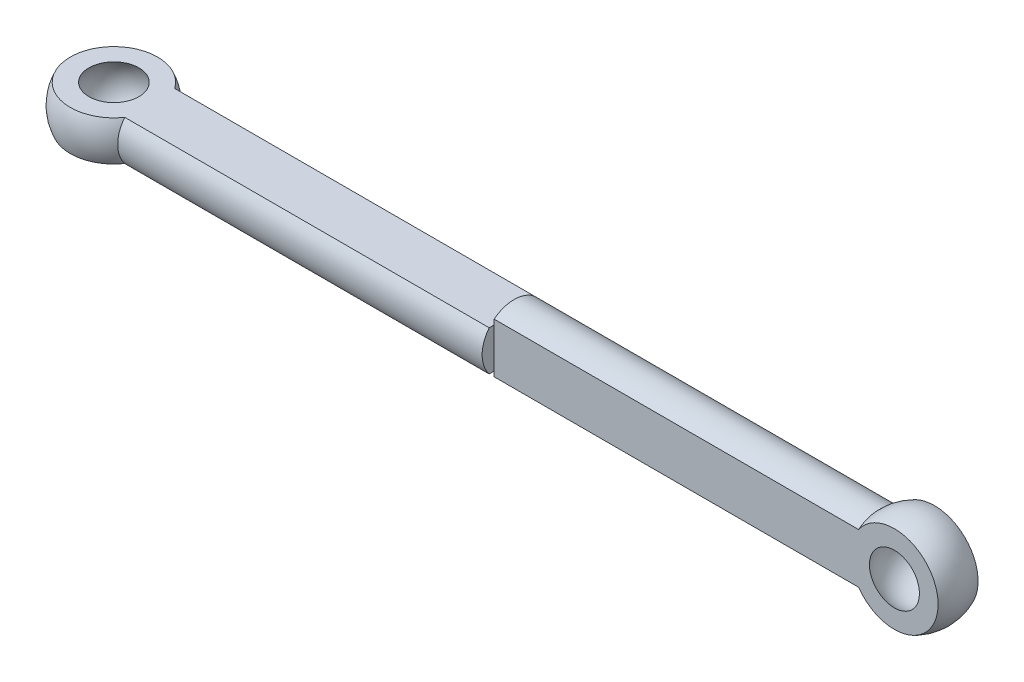
SolidWorks part; units mm, degrees
ref_plane "Front Plane" through (0, 0, 0) normal (0, 0, 1) x (1, 0, 0)
ref_plane "Top Plane" through (0, 0, 0) normal (0, 1, 0) x (1, 0, 0)
ref_plane "Right Plane" through (0, 0, 0) normal (1, 0, 0) x (0, 0, -1)
sketch "Sketch1" plane through (0, 0, 0) normal (0, 1, 0) x (1, 0, 0)
  line L0 (25, 0) -> (0, 0) construction
  line L1 (0, 0) -> (-25, 0) construction
  dimension "D1" = 25
sketch "Sketch2" plane through (0, 0, 0) normal (0, 1, 0) x (1, 0, 0)
  line L0 (0, 0) -> (-25, 0) construction
  line L1 (-28, 0) -> (-27, 0)
  line L2 (-23, 0) -> (23, 0)
  line L3 (25, 0) -> (0, 0) construction
  line L4 (-22.7639, -2) -> (22.7639, -2)
  line L5 (0, -2) -> (0, 0)
  line L6 (28, 0) -> (27, 0)
  arc A0 (-27, 0) -> (-23, 0) centre (-25, 0) ccw
  arc A1 (-28, 0) -> (-22.7639, -2) centre (-25, 0) ccw
  arc A2 (28, 0) -> (22.7639, -2) centre (25, 0) cw
  arc A3 (27, 0) -> (23, 0) centre (25, 0) cw
  dimension "D2" = 2
  dimension "D3" = 3
  dimension "D1" = 2
revolve "Revolve1" add sketch "Sketch2" angle 360 about L1
sketch "Sketch3" plane through (0, 0, 0) normal (1, 0, 0) x (0, 0, -1)
  line L1 (-3, 1.25) -> (3, 1.25)
  line L2 (-3, 1.25) -> (-3, -1.25)
  line L3 (-3, -1.25) -> (3, -1.25)
  line L4 (3, 1.25) -> (3, -1.25)
  line L5 (-3, 1.25) -> (3, -1.25) construction
  line L6 (-3, -1.25) -> (3, 1.25) construction
  point P0 (0, 0)
  dimension "D1" = 2.5
  dimension "D2" = 6
extrude "Cut-Extrude2" cut sketch "Sketch3" against normal blind 60 flip side to cut
sketch "Sketch5" plane through (0, 0, 0) normal (1, 0, 0) x (0, 0, -1)
  line L1 (-1.25, 3) -> (1.25, 3)
  line L2 (-1.25, 3) -> (-1.25, -3)
  line L3 (-1.25, -3) -> (1.25, -3)
  line L4 (1.25, 3) -> (1.25, -3)
  line L5 (-1.25, 3) -> (1.25, -3) construction
  line L6 (-1.25, -3) -> (1.25, 3) construction
  point P0 (0, 0)
  dimension "D1" = 6
  dimension "D2" = 2.5
extrude "Cut-Extrude3" cut sketch "Sketch5" along normal through all flip side to cut
